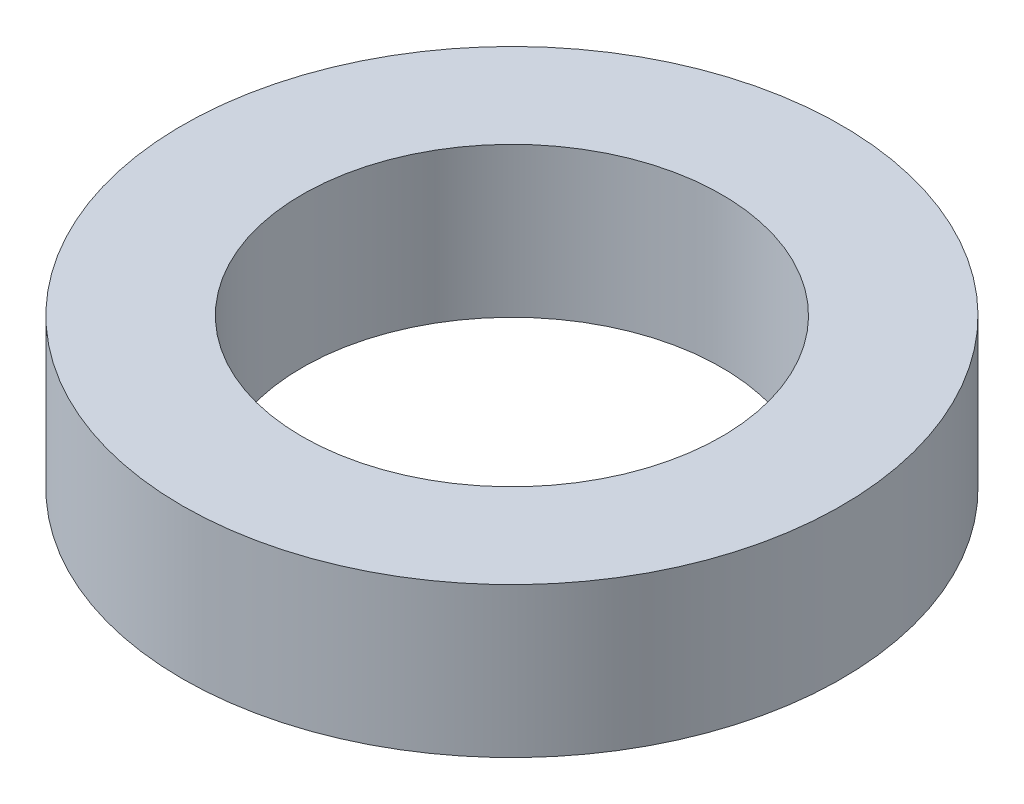
SolidWorks part; units mm, degrees
ref_plane "前视基准面" through (0, 0, 0) normal (0, 0, 1) x (1, 0, 0)
ref_plane "上视基准面" through (0, 0, 0) normal (0, 1, 0) x (1, 0, 0)
ref_plane "右视基准面" through (0, 0, 0) normal (1, 0, 0) x (0, 0, -1)
sketch "草图1" plane through (0, 0, 0) normal (0, 1, 0) x (1, 0, 0)
  circle A0 centre (0, 0) radius 5.5
  circle A1 centre (0, 0) radius 3.5
extrude "凸台-拉伸1" add sketch "草图1" along normal blind 2.5
